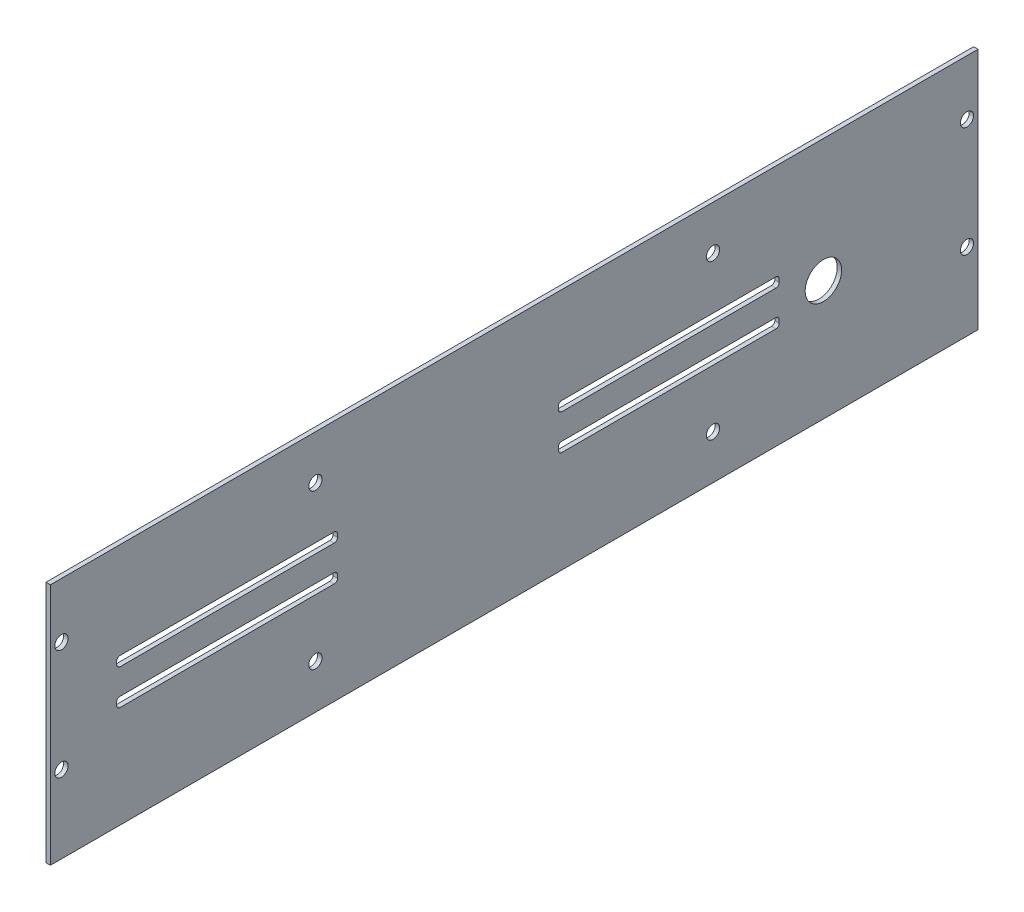
SolidWorks part; units mm, degrees
ref_plane "Front Plane" through (0, 0, 0) normal (0, 0, 1) x (1, 0, 0)
ref_plane "Top Plane" through (0, 0, 0) normal (0, 1, 0) x (1, 0, 0)
ref_plane "Right Plane" through (0, 0, 0) normal (1, 0, 0) x (0, 0, -1)
sketch "Sketch1" plane through (23.9483, 0, 0) normal (1, 0, 0) x (0, 0, -1)
  line L0 (40.8078, -10) -> (-410.1922, -10) construction
  line L1 (-394.6922, 100) -> (25.3078, 100)
  line L2 (-394.6922, 100) -> (-394.6922, -10)
  line L3 (-394.6922, -10) -> (25.3078, -10)
  line L4 (25.3078, 100) -> (25.3078, -10)
  line L5 (45.3078, 0) -> (45.3078, -10) construction
  dimension "D1" = 20
extrude "Boss-Extrude1" add sketch "Sketch1" along normal blind 2
sketch "Sketch2" plane through (25.9483, 0, 0) normal (1, 0, 0) x (0, 0, -1)
  line L0 (25.3078, 100) -> (-394.6922, 100) construction
  line L1 (-364.6922, 52.1) -> (-264.6922, 52.1)
  line L2 (-364.6922, 52.1) -> (-364.6922, 56.5)
  line L3 (-364.6922, 56.5) -> (-264.6922, 56.5)
  line L4 (-264.6922, 52.1) -> (-264.6922, 56.5)
  line L5 (-364.6922, 40.5) -> (-264.6922, 40.5)
  line L6 (-364.6922, 40.5) -> (-364.6922, 36.1)
  line L7 (-364.6922, 36.1) -> (-264.6922, 36.1)
  line L8 (-264.6922, 40.5) -> (-264.6922, 36.1)
  line L9 (-64.6922, 56.5) -> (-164.6922, 56.5)
  line L10 (-64.6922, 56.5) -> (-64.6922, 52.1)
  line L11 (-64.6922, 52.1) -> (-164.6922, 52.1)
  line L12 (-164.6922, 56.5) -> (-164.6922, 52.1)
  line L13 (-164.6922, 40.5) -> (-64.6922, 40.5)
  line L14 (-164.6922, 40.5) -> (-164.6922, 36.1)
  line L15 (-164.6922, 36.1) -> (-64.6922, 36.1)
  line L16 (-64.6922, 40.5) -> (-64.6922, 36.1)
  line L17 (-394.6922, 100) -> (-394.6922, -10) construction
  dimension "D1" = 100
  dimension "D2" = 100
  dimension "D3" = 100
  dimension "D4" = 100
  dimension "D5" = 4.4
  dimension "D6" = 4.4
  dimension "D7" = 4.4
  dimension "D8" = 4.4
  dimension "D9" = 11.6
  dimension "D10" = 11.6
  dimension "D11" = 43.5
  dimension "D12" = 43.5
  dimension "D13" = 30
  dimension "D14" = 30
  dimension "D15" = 100
  dimension "D16" = 100
extrude "Cut-Extrude1" cut sketch "Sketch2" against normal blind 2
fillet "Fillet1" radius 1.5 16 edges at (24.9483, 40.5, 64.6922) (24.9483, 36.1, 64.6922) (24.9483, 52.1, 64.6922) (24.9483, 56.5, 64.6922) (24.9483, 36.1, 164.6922) (24.9483, 40.5, 164.6922) (24.9483, 52.1, 164.6922) (24.9483, 56.5, 164.6922) (24.9483, 36.1, 264.6922) (24.9483, 40.5, 264.6922) (24.9483, 52.1, 264.6922) (24.9483, 56.5, 264.6922) (24.9483, 36.1, 364.6922) (24.9483, 40.5, 364.6922) (24.9483, 52.1, 364.6922) (24.9483, 56.5, 364.6922)
sketch "Sketch3" plane through (25.9483, 0, 0) normal (1, 0, 0) x (0, 0, -1)
  circle A0 centre (-389.6922, 75) radius 3
  circle A1 centre (-389.6922, 25) radius 3
  circle A2 centre (20.3078, 75) radius 3
  circle A3 centre (20.3078, 25) radius 3
  dimension "D1" = 6
extrude "Cut-Extrude2" cut sketch "Sketch3" against normal up to next
sketch "Sketch4" plane through (25.9483, 0, 0) normal (1, 0, 0) x (0, 0, -1)
  line L0 (-394.6922, -10) -> (25.3078, -10) construction
  line L1 (-394.6922, 100) -> (-394.6922, -10) construction
  line L2 (25.3078, -10) -> (25.3078, 100) construction
  line L3 (25.3078, 100) -> (-394.6922, 100) construction
  circle A0 centre (-274.6922, 10) radius 3
  circle A1 centre (-94.6922, 10) radius 3
  circle A2 centre (-44.6922, 44.3) radius 8.25
  circle A3 centre (-274.6922, 80) radius 3
  circle A4 centre (-94.6922, 80) radius 3
  dimension "D1" = 6
  dimension "D2" = 6
  dimension "D7" = 16.5
  dimension "D10" = 6
  dimension "D11" = 6
  dimension "D3" = 20
  dimension "D4" = 120
  dimension "D5" = 120
  dimension "D6" = 20
  dimension "D8" = 70
  dimension "D9" = 54.3
  dimension "D12" = 20
  dimension "D13" = 20
  dimension "D14" = 120
  dimension "D15" = 120
extrude "Cut-Extrude3" cut sketch "Sketch4" against normal up to next
